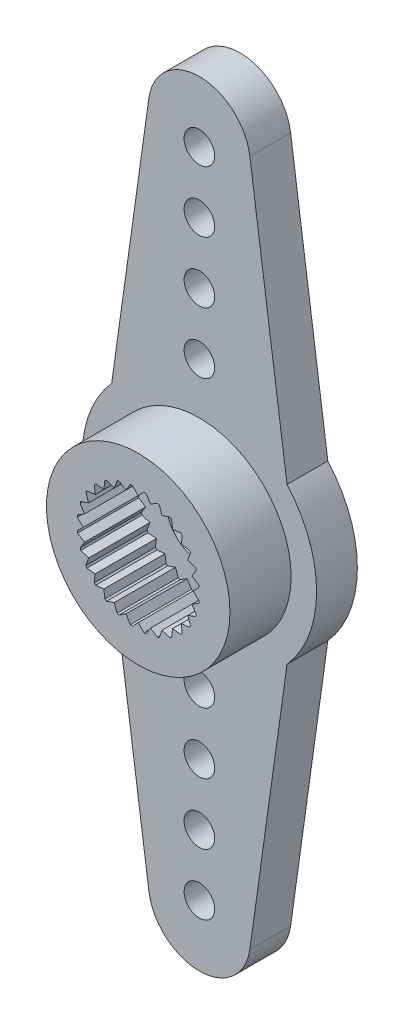
SolidWorks part; units mm, degrees
ref_plane "Plan de face" through (0, 0, 0) normal (0, 0, 1) x (1, 0, 0)
ref_plane "Plan de dessus" through (0, 0, 0) normal (0, 1, 0) x (1, 0, 0)
ref_plane "Plan de droite" through (0, 0, 0) normal (1, 0, 0) x (0, 0, -1)
sketch "Esquisse1" plane through (0, 0, 0) normal (0, 0, 1) x (1, 0, 0)
  circle A0 centre (0, 0) radius 5.75
  circle A1 centre (0, 0) radius 1.6
  dimension "D1" = 11.5
  dimension "D2" = 3.2
extrude "Boss.-Extru.1" add sketch "Esquisse1" along normal blind 5
sketch "Esquisse2" plane through (0, 0, 5) normal (0, 0, 1) x (1, 0, 0)
  circle A0 centre (0, 0) radius 3
  dimension "D1" = 6
extrude "Enlèv. mat.-Extru.1" cut sketch "Esquisse2" against normal blind 3
sketch "Esquisse3" plane through (0, 0, 5) normal (0, 0, 1) x (1, 0, 0)
  circle A0 centre (0, 0) radius 5.75
  circle A1 centre (0, 0) radius 4.5
  circle A2 centre (0, 0) radius 3 construction
  circle A3 centre (0, 0) radius 5.75 construction
  dimension "D1" = 1.5
extrude "Enlèv. mat.-Extru.2" cut sketch "Esquisse3" against normal blind 3
sketch "Esquisse4" plane through (0, 0, 0) normal (0, 0, -1) x (-1, 0, 0)
  line L0 (-4.3, 3.8174) -> (-2.4759, 16.8466)
  line L1 (2.4759, 16.8466) -> (4.3, 3.8174)
  line L2 (-5.2729, 19) -> (6.8365, 19) construction
  line L3 (0, 0) -> (0, 24.2526) construction
  circle A0 centre (0, 0) radius 5.75 construction
  arc A1 (-2.4759, 16.8466) -> (2.4759, 16.8466) centre (0, 16.5) cw
  arc A2 (-4.3, 3.8174) -> (4.3, 3.8174) centre (0, 0) cw
  dimension "D2" = 2.5
  dimension "D1" = 8.6
  dimension "D3" = 19
extrude "Boss.-Extru.2" add sketch "Esquisse4" against normal up to surface (2 mm away) up to face at (4.5, 0, 2)
pattern_circular "Répétition circulaire1" count 2 every 180 about axis through (0, 0, 0) along (0, 0, 1) of "Boss.-Extru.2"
sketch "Esquisse5" plane through (0, 0, 0) normal (0, 0, -1) x (-1, 0, 0)
  line L0 (0, 0) -> (0, 20.4605) construction
  circle A0 centre (0, 7) radius 0.75
  circle A1 centre (0, 10) radius 0.75
  circle A2 centre (0, 13) radius 0.75
  circle A3 centre (0, 16) radius 0.75
  dimension "D5" = 1.5
  dimension "D6" = 1.5
  dimension "D7" = 1.5
  dimension "D8" = 1.5
  dimension "D1" = 7
  dimension "D2" = 3
  dimension "D3" = 3
  dimension "D4" = 3
extrude "Enlèv. mat.-Extru.3" cut sketch "Esquisse5" against normal blind 3
pattern_circular "Répétition circulaire2" count 2 every 180 about axis through (0, 0, 0) along (0, 0, 1) of "Enlèv. mat.-Extru.3"
sketch "Esquisse6" plane through (0, 0, 5) normal (0, 0, 1) x (1, 0, 0)
  line L0 (-1.598, 3) -> (1.8482, 3) construction
  line L1 (0, 0) -> (0, 5.9454) construction
  line L2 (-0.3, 3) -> (0, 2.7)
  line L3 (0, 2.7) -> (0.3, 3)
  line L4 (0.3, 3) -> (-0.3, 3)
  circle A0 centre (0, 0) radius 3 construction
  dimension "D1" = 0.3
  dimension "D2" = 0.6
extrude "Boss.-Extru.3" add sketch "Esquisse6" against normal up to surface (3 mm away) up to face at (1.6, 0, 2)
pattern_circular "Répétition circulaire3" count 28 over 360 about axis through (0, 0, 0) along (0, 0, 1) of "Boss.-Extru.3"
sketch "Esquisse7" plane through (0, 0, 0) normal (0, 0, -1) x (-1, 0, 0)
  circle A0 centre (0, 0) radius 1.6
  circle A1 centre (0, 0) radius 3
  circle A2 centre (0, 0) radius 1.6 construction
  dimension "D1" = 6
extrude "Enlèv. mat.-Extru.4" cut sketch "Esquisse7" against normal blind 1
sketch "Esquisse8" plane through (0, 0, 0) normal (0, 0, -1) x (-1, 0, 0)
  circle A0 centre (0, 0) radius 3.4
  circle A1 centre (0, 0) radius 4.7
  circle A2 centre (0, 0) radius 3 construction
  dimension "D1" = 0.4
  dimension "D2" = 1.3
extrude "Enlèv. mat.-Extru.5" cut sketch "Esquisse8" against normal blind 1
